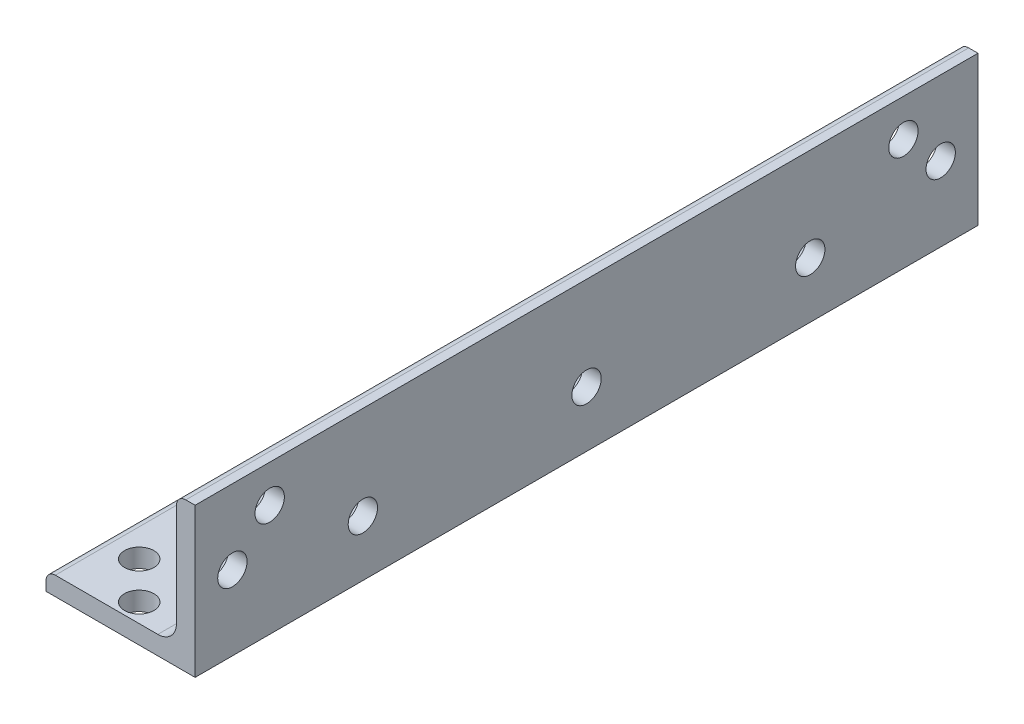
SolidWorks part; units mm, degrees
ref_plane "Front Plane" through (0, 0, 0) normal (0, 0, 1) x (1, 0, 0)
ref_plane "Top Plane" through (0, 0, 0) normal (0, 1, 0) x (1, 0, 0)
ref_plane "Right Plane" through (0, 0, 0) normal (1, 0, 0) x (0, 0, -1)
sketch "Sketch0" plane through (0, 0, 0) normal (0, 0, 1) x (1, 0, 0)
  line L0 (-12.7, -12.7) -> (12.7, -12.7)
  line L1 (12.7, -12.7) -> (12.7, 12.7)
  line L2 (12.7, 0) -> (0, 0) construction
  line L3 (0, 0) -> (0, -12.7) construction
  line L4 (9.525, -6.35) -> (9.525, 12.7) construction
  line L5 (6.35, -9.525) -> (-12.7, -9.525) construction
  arc A0 (9.525, -6.35) -> (6.35, -9.525) centre (6.35, -6.35) cw
  point P3 (8.5951, -8.5951)
  dimension "Inside Corner Radius" = 3.175
  dimension "Outside Height" = 25.4
  dimension "Inside Height" = 22.225
  dimension "Inside Width" = 22.225
  dimension "Wall Thickness" = 3.175
  dimension "D1" = 3.175
  dimension "Outside Width" = 25.4
sketch "Sketch1" plane through (0, 0, 0) normal (1, 0, 0) x (0, 0, -1)
  line L0 (304.8, 0) -> (-304.8, 0)
  point P4 (0, 0)
  dimension "Length" = 609.6
sketch "Sketch2" plane through (0, 0, 0) normal (0, 0, 1) x (1, 0, 0)
  line L0 (-12.7, -12.7) -> (12.7, -12.7)
  line L1 (12.7, -12.7) -> (12.7, 12.7)
  line L2 (12.7, 12.7) -> (9.525, 12.7) construction
  line L3 (9.525, 11.1125) -> (9.525, -6.35)
  line L4 (6.35, -9.525) -> (-11.1125, -9.525)
  line L5 (-12.7, -12.7) -> (-12.7, -9.525) construction
  line L6 (11.1125, 12.7) -> (12.7, 12.7)
  line L7 (-12.7, -11.1125) -> (-12.7, -12.7)
  line L8 (12.7, 0) -> (0, 0) construction
  line L9 (0, 0) -> (0, -12.7) construction
  arc A0 (9.525, 11.1125) -> (11.1125, 12.7) centre (11.1125, 11.1125) cw
  arc A1 (-12.7, -11.1125) -> (-11.1125, -9.525) centre (-11.1125, -11.1125) cw
  arc A2 (9.525, -6.35) -> (6.35, -9.525) centre (6.35, -6.35) cw
  dimension "Inside Radius" = 3.175
  dimension "Height" = 25.4
  dimension "Width" = 25.4
  dimension "Thickness" = 3.175
extrude "Boss-Extrude1" add sketch "Sketch2" along normal mid plane 609.6
sketch "Break Locations" plane through (0, 0, 0) normal (1, 0, 0) x (0, 0, -1)
  line L0 (-278.892, 0) -> (278.892, 0)
  line L1 (-304.8, -12.7) -> (-304.8, 12.7) construction
  line L2 (304.8, -12.7) -> (304.8, 12.7) construction
  point P0 (-283.21, 0)
  point P1 (283.21, 0)
  point P10 (0, 0)
  point P11 (278.892, 0)
  point P13 (-278.892, 0)
  dimension "D1" = 21.59
  dimension "D2" = 21.59
  dimension "D3" = 25.908
sketch "Sketch7" plane through (0, -12.7, 0) normal (0, -1, 0) x (1, 0, 0)
  line L0 (-12.7, -171.45) -> (12.7, -171.45)
  line L1 (-12.7, 304.8) -> (12.7, 304.8)
  line L2 (-12.7, 304.8) -> (-12.7, -304.8)
  line L3 (-12.7, -304.8) -> (12.7, -304.8)
  line L4 (12.7, 304.8) -> (12.7, -304.8)
  line M4 (12.7, -304.8) -> (12.7, 304.8)
  line M5 (12.7, 304.8) -> (-12.7, 304.8)
  line M6 (-12.7, 304.8) -> (-12.7, -304.8)
  dimension "D1" = 133.35
extrude "Cut-Extrude1" cut sketch "Sketch7" against normal blind 254 contours L0 M6 M4 M5
sketch "Sketch3" plane through (0, 0, 0) normal (0, 1, 0) x (1, 0, 0)
  line L0 (12.7, 171.45) -> (12.7, 304.8) construction
  line L1 (-12.7, 304.8) -> (12.7, 304.8) construction
  line L2 (12.7, 171.45) -> (12.7, 304.8) construction
  line L4 (-11.1125, 238.125) -> (6.35, 238.125) construction
  line L5 (-11.1125, 171.45) -> (-11.1125, 304.8) construction
  line L6 (6.35, 171.45) -> (6.35, 304.8) construction
  line L7 (3.175, 276.225) -> (3.175, 238.125) construction
  circle A0 centre (-6.35, 295.275) radius 2.5
  circle A1 centre (0, 301.625) radius 2.5
  circle A2 centre (3.175, 276.225) radius 2.5
  circle A3 centre (3.175, 238.125) radius 2.5
  circle A4 centre (3.175, 200.025) radius 2.5
  circle A13 centre (0, 174.625) radius 2.5
  circle A14 centre (-6.35, 180.975) radius 2.5
  point P12 (3.175, 238.125)
  dimension "D3" = 5
  dimension "D1" = 12.7
  dimension "D2" = 3.175
  dimension "D4" = 19.05
  dimension "D5" = 9.525
  dimension "D6" = 9.525
  dimension "D9" = 38.1
  dimension "D8" = 3
extrude "Cut-Extrude2" cut sketch "Sketch3" against normal blind 254
sketch "Sketch8" plane through (12.7, 0, -12.7) normal (-1, 0, 0) x (0, 0, 1)
  line L0 (-158.75, -6.35) -> (-292.1, -6.35) construction
  line L1 (-158.75, 11.1125) -> (-292.1, 11.1125) construction
  line L2 (-158.75, -12.7) -> (-292.1, -12.7) construction
  line L3 (-292.1, 11.1125) -> (-292.1, -6.35) construction
  line L4 (-225.425, 11.1125) -> (-225.425, -6.35) construction
  line L7 (-187.325, -3.175) -> (-225.425, -3.175) construction
  circle A0 centre (-171.45, 6.35) radius 2.5
  circle A1 centre (-165.1, 0) radius 2.5
  circle A2 centre (-187.325, -3.175) radius 2.5
  circle A3 centre (-225.425, -3.175) radius 2.5
  circle A4 centre (-263.525, -3.175) radius 2.5
  circle A13 centre (-285.75, 0) radius 2.5
  circle A14 centre (-279.4, 6.35) radius 2.5
  point P4 (0, 0)
  dimension "D3" = 5
  dimension "D1" = 9.525
  dimension "D2" = 12.7
  dimension "D4" = 6.35
  dimension "D5" = 19.05
  dimension "D6" = 12.7
  dimension "D9" = 38.1
  dimension "D8" = 3
extrude "Cut-Extrude4" cut sketch "Sketch8" along normal blind 254
equation "\"D1@Break Locations\" = .85 * \"Height@Sketch2\""
equation "\"D2@Break Locations\"=\"D1@Break Locations\""
equation "\"Thickness@Sketch2\" = \"Wall Thickness@Sketch0\""
equation "\"Height@Sketch2\" = \"Outside Height@Sketch0\""
equation "\"Width@Sketch2\" = \"Outside Width@Sketch0\""
equation "\"Inside Radius@Sketch2\" = \"Inside Corner Radius@Sketch0\""
equation "\"Length@Boss-Extrude1\" = \"Length@Sketch1\""
equation "\"D3@Break Locations\"=\"D2@Break Locations\"*1.2"
equation "\"D1@Sketch0\"=\"Wall Thickness@Sketch0\""
